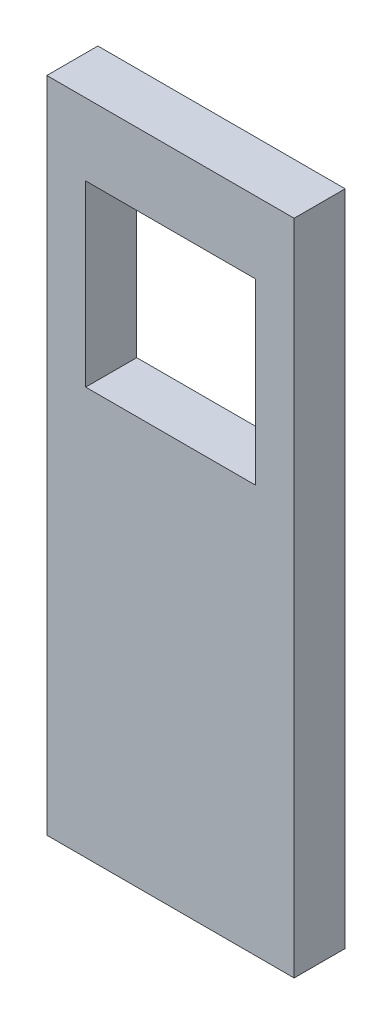
SolidWorks part; units mm, degrees
ref_plane "Front Plane" through (0, 0, 0) normal (0, 0, 1) x (1, 0, 0)
ref_plane "Top Plane" through (0, 0, 0) normal (0, 1, 0) x (1, 0, 0)
ref_plane "Right Plane" through (0, 0, 0) normal (1, 0, 0) x (0, 0, -1)
sketch "Sketch1" plane through (0, 0, 0) normal (0, 0, 1) x (1, 0, 0)
  line L0 (0, 66.85) -> (0, 44.55) construction
  line L1 (0, 66.85) -> (25, 66.85) construction
  line L2 (0, 44.55) -> (0, 39.4) construction
  line L3 (25, 0) -> (0, 0) construction
  line L4 (3.96, 59.525) -> (21.04, 59.525) construction
  line L5 (3.96, 41.525) -> (21.04, 41.525) construction
  line L6 (3.96, 59.525) -> (3.96, 41.525) construction
  line L7 (21.04, 59.525) -> (21.04, 41.525) construction
  line L8 (0, 44.55) -> (25, 44.55) construction
  line L9 (0, 39.4) -> (25, 39.4) construction
  line L10 (0, 39.4) -> (0, 27.45) construction
  line L11 (0, 27.45) -> (0, 22.3) construction
  line L12 (25, 44.55) -> (25, 39.4) construction
  line L13 (25, 66.85) -> (25, 44.55) construction
  line L14 (0, 22.3) -> (0, 0) construction
  line L15 (25, 39.4) -> (25, 27.45) construction
  line L16 (25, 27.45) -> (25, 22.3) construction
  line L17 (25, 22.3) -> (25, 0) construction
  line L18 (0, 27.45) -> (25, 27.45) construction
  line L19 (25, 22.3) -> (0, 22.3) construction
  line L20 (12.5, -0.0005) -> (12.5, 4.0956) construction
  line L21 (-0.1, 66.95) -> (-0.1, 44.55)
  line L22 (-0.1, 44.55) -> (-0.1, 39.4)
  line L23 (-0.1, 39.4) -> (-0.1, 27.45)
  line L24 (-0.1, 27.45) -> (-0.1, 22.3)
  line L25 (-0.1, 22.3) -> (-0.1, -0.1)
  line L26 (25.1, -0.1) -> (-0.1, -0.1)
  line L27 (25.1, 22.3) -> (25.1, -0.1)
  line L28 (25.1, 27.45) -> (25.1, 22.3)
  line L29 (25.1, 39.4) -> (25.1, 27.45)
  line L30 (25.1, 44.55) -> (25.1, 39.4)
  line L31 (25.1, 66.95) -> (25.1, 44.55)
  line L32 (-0.1, 66.95) -> (25.1, 66.95)
  line L33 (21.14, 59.625) -> (21.14, 41.425)
  line L34 (3.86, 41.425) -> (21.14, 41.425)
  line L35 (3.86, 59.625) -> (3.86, 41.425)
  line L36 (3.86, 59.625) -> (21.14, 59.625)
  point P18 (12.5, 41.525)
  point P20 (12.5, 59.525)
  point P21 (12.5, 66.85)
  dimension "D1" = 3.025
  dimension "D2" = 11.95
  dimension "D3" = 5.15
  dimension "D4" = 25
  dimension "D5" = 18
  dimension "D6" = 17.08
  dimension "D7" = 22.3
  dimension "D8" = 0.1
  dimension "D9" = 0.1
extrude "Boss-Extrude1" add sketch "Sketch1" along normal mid plane 5.2
